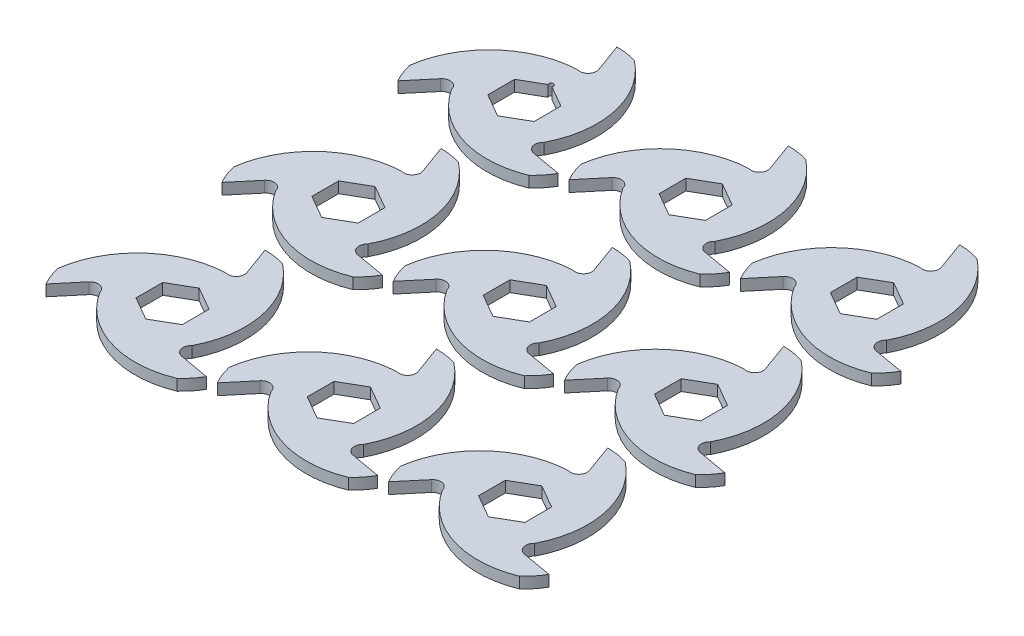
SolidWorks part; units mm, degrees
ref_plane "Front Plane" through (0, 0, 0) normal (0, 0, 1) x (1, 0, 0)
ref_plane "Top Plane" through (0, 0, 0) normal (0, 1, 0) x (1, 0, 0)
ref_plane "Right Plane" through (0, 0, 0) normal (1, 0, 0) x (0, 0, -1)
sketch "Sketch2" plane through (0, 0, 0) normal (0, 1, 0) x (1, 0, 0)
  line L0 (0, 50.8) -> (0, 0) construction
  line L1 (0, 0) -> (-43.9941, -25.4) construction
  line L2 (0, 0) -> (43.9941, -25.4) construction
  line L3 (0, 50.8) -> (5.6992, 35.1416)
  line L4 (43.9941, -25.4) -> (27.5839, -22.5064)
  line L5 (-43.9941, -25.4) -> (-33.2831, -12.6352)
  line L7 (0, 14.6647) -> (-12.7, 7.3323)
  line L8 (-12.7, 7.3323) -> (-12.7, -7.3323)
  line L9 (-12.7, -7.3323) -> (0, -14.6647)
  line L10 (0, -14.6647) -> (12.7, -7.3323)
  line L11 (12.7, -7.3323) -> (12.7, 7.3323)
  line L12 (12.7, 7.3323) -> (0, 14.6647)
  circle A0 centre (0, 0) radius 50.8 construction
  circle A1 centre (0, 13.2055) radius 37.5945
  circle A2 centre (11.4363, -6.6028) radius 37.5945
  circle A3 centre (-11.4363, -6.6028) radius 37.5945
  arc A4 (5.6992, 35.1416) -> (0, 29.21) centre (1.3938, 33.5746) cw
  arc A5 (27.5839, -22.5064) -> (25.2966, -14.605) centre (28.3796, -17.9943) cw
  arc A6 (-33.2831, -12.6352) -> (-25.2966, -14.605) centre (-29.7733, -15.5803) cw
  circle A7 centre (0, 0) radius 12.7 construction
  point P25 (0, 0)
  dimension "D1" = 101.6
  dimension "D4" = 20
  dimension "D2" = 120
  dimension "D3" = 120
  dimension "D5" = 21.59
  dimension "D8" = 25.4
  dimension "D7" = 3
extrude "Boss-Extrude2" add sketch "Sketch2" along normal mid plane 6.096 contours A1 A3 A2 L12 L11 L10 L9 L8 L7 | A1 A6 A2 A3 | L5 A6 A1 A3 | L4 A5 A3 A2 | A3 A5 A1 A2 | A2 A4 A3 A1 | L3 A4 A2 A1
sketch "Sketch3" plane through (0, 3.048, 0) normal (0, 1, 0) x (1, 0, 0)
  line L3 (43.9941, -25.4) -> (27.5839, -22.5064)
  line L4 (0, 50.8) -> (5.6992, 35.1416)
  line L5 (-43.9941, -25.4) -> (-33.2831, -12.6352)
  line L6 (43.9941, -25.4) -> (27.5839, -22.5064)
  line L7 (0, 50.8) -> (5.6992, 35.1416)
  line L8 (-43.9941, -25.4) -> (-33.2831, -12.6352)
  arc A0 (-48.1379, -14.7476) -> (0, 29.21) centre (2.2057, -21.5421) cw
  arc A1 (0, 29.21) -> (-43.9941, -25.4) centre (-11.4363, -6.6028) ccw construction
  arc A2 (0, 29.21) -> (5.6992, 35.1416) centre (1.3938, 33.5746) ccw construction
  arc A3 (11.2972, 49.0624) -> (25.2966, -14.605) centre (-19.7588, 8.8609) cw
  arc A4 (36.8407, -34.3148) -> (-25.2966, -14.605) centre (17.5532, 12.6812) cw
  arc A9 (-25.2966, -14.605) -> (-33.2831, -12.6352) centre (-29.7733, -15.5803) ccw
  arc A10 (-25.2966, -14.605) -> (43.9941, -25.4) centre (11.4363, -6.6028) ccw
  arc A11 (25.2966, -14.605) -> (27.5839, -22.5064) centre (28.3796, -17.9943) ccw
  arc A12 (25.2966, -14.605) -> (0, 50.8) centre (0, 13.2055) ccw
  arc A13 (0, 29.21) -> (5.6992, 35.1416) centre (1.3938, 33.5746) ccw
  arc A14 (0, 29.21) -> (-43.9941, -25.4) centre (-11.4363, -6.6028) ccw
  arc A15 (-25.2966, -14.605) -> (-33.2831, -12.6352) centre (-29.7733, -15.5803) ccw
  arc A16 (-25.2966, -14.605) -> (43.9941, -25.4) centre (11.4363, -6.6028) ccw
  arc A17 (25.2966, -14.605) -> (27.5839, -22.5064) centre (28.3796, -17.9943) ccw
  arc A18 (25.2966, -14.605) -> (0, 50.8) centre (0, 13.2055) ccw
  arc A19 (0, 29.21) -> (5.6992, 35.1416) centre (1.3938, 33.5746) ccw
  arc A20 (0, 29.21) -> (-43.9941, -25.4) centre (-11.4363, -6.6028) ccw
  point P26 (0, 0)
  arc M20 (-25.2966, -14.605) -> (43.9941, -25.4) centre (11.4363, -6.6028) ccw
  arc M23 (25.2966, -14.605) -> (0, 50.8) centre (0, 13.2055) ccw
  arc M26 (0, 29.21) -> (-43.9941, -25.4) centre (-11.4363, -6.6028) ccw
  dimension "D3" = 50.8
  dimension "D1" = 11.43
  dimension "D2" = 0
  dimension "D4" = 3
extrude "Cut-Extrude1" cut sketch "Sketch3" against normal through all contours A0 M26 | A3 M23 | A4 M20
pattern_linear "LPattern1" count 3 spacing 96.52 along (0, 0, 1) count 3 spacing 93.98 along (1, 0, 0) of "Boss-Extrude2"
sketch "Sketch4" plane through (0, 3.048, 0) normal (0, 1, 0) x (1, 0, 0)
  circle A0 centre (0, 14.6647) radius 1.27
  dimension "D1" = 2.54
extrude "Cut-Extrude2" cut sketch "Sketch4" against normal through all
